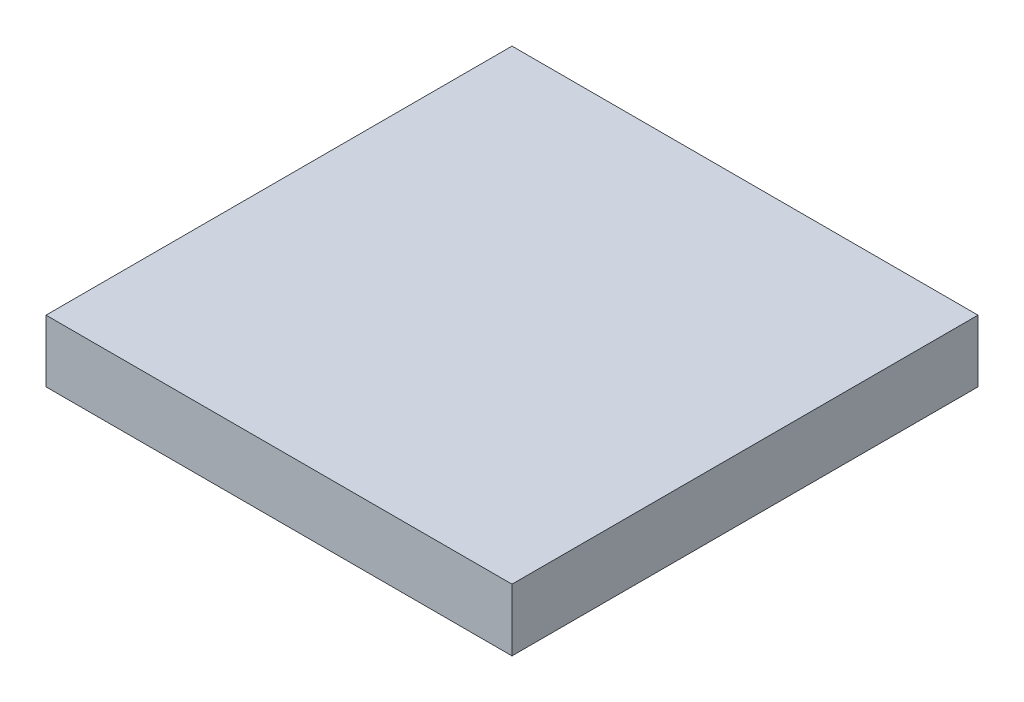
SolidWorks part; units mm, degrees
ref_plane "Front Plane" through (0, 0, 0) normal (0, 0, 1) x (1, 0, 0)
ref_plane "Top Plane" through (0, 0, 0) normal (0, 1, 0) x (1, 0, 0)
ref_plane "Right Plane" through (0, 0, 0) normal (1, 0, 0) x (0, 0, -1)
sketch "Sketch1" plane through (0, 0, 0) normal (0, 1, 0) x (1, 0, 0)
  line L0 (0, 0) -> (18.6879, 0) construction
  line L1 (0, 0) -> (0, -14.4281) construction
  line L3 (-1.5, 1.5) -> (1.5, 1.5)
  line L4 (-1.5, 1.5) -> (-1.5, -1.5)
  line L5 (-1.5, -1.5) -> (1.5, -1.5)
  line L6 (1.5, 1.5) -> (1.5, -1.5)
  dimension "D1" = 3
  dimension "D2" = 3
extrude "Boss-Extrude1" add sketch "Sketch1" along normal blind 0.4
